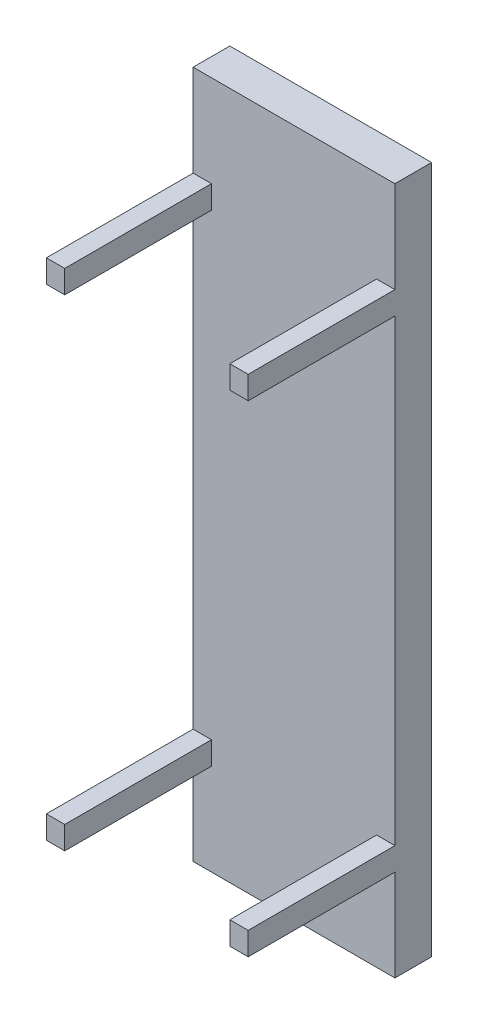
SolidWorks part; units mm, degrees
ref_plane "Front Plane" through (0, 0, 0) normal (0, 0, 1) x (1, 0, 0)
ref_plane "Top Plane" through (0, 0, 0) normal (0, 1, 0) x (1, 0, 0)
ref_plane "Right Plane" through (0, 0, 0) normal (1, 0, 0) x (0, 0, -1)
sketch "Sketch1" plane through (0, 0, 0) normal (0, 0, 1) x (1, 0, 0)
  line L0 (-220, 750) -> (220, 750)
  line L2 (-220, 750) -> (-220, -750)
  line L3 (-220, -750) -> (220, -750)
  line L4 (220, -750) -> (220, 750)
extrude "Boss-Extrude1" add sketch "Sketch1" along normal blind 80
sketch "Sketch4" plane through (0, 0, 80) normal (0, 0, 1) x (1, 0, 0)
  line L1 (-220, 750) -> (-220, -750) construction
  line L2 (-220, 550) -> (-180, 550)
  line L3 (-180, 550) -> (-180, 500)
  line L4 (-180, 500) -> (-220, 500)
  line L5 (-220, 500) -> (-220, 550)
  line L10 (-220, -500) -> (-220, -550)
  line L11 (-180, -500) -> (-220, -500)
  line L12 (-180, -550) -> (-180, -500)
  line L13 (-220, -550) -> (-180, -550)
  line L14 (220, -550) -> (180, -550)
  line L15 (180, -550) -> (180, -500)
  line L16 (180, -500) -> (220, -500)
  line L17 (220, -500) -> (220, -550)
  line L18 (220, 500) -> (220, 550)
  line L19 (180, 500) -> (220, 500)
  line L20 (180, 550) -> (180, 500)
  line L21 (220, 550) -> (180, 550)
extrude "Boss-Extrude4" add sketch "Sketch4" along normal blind 320
